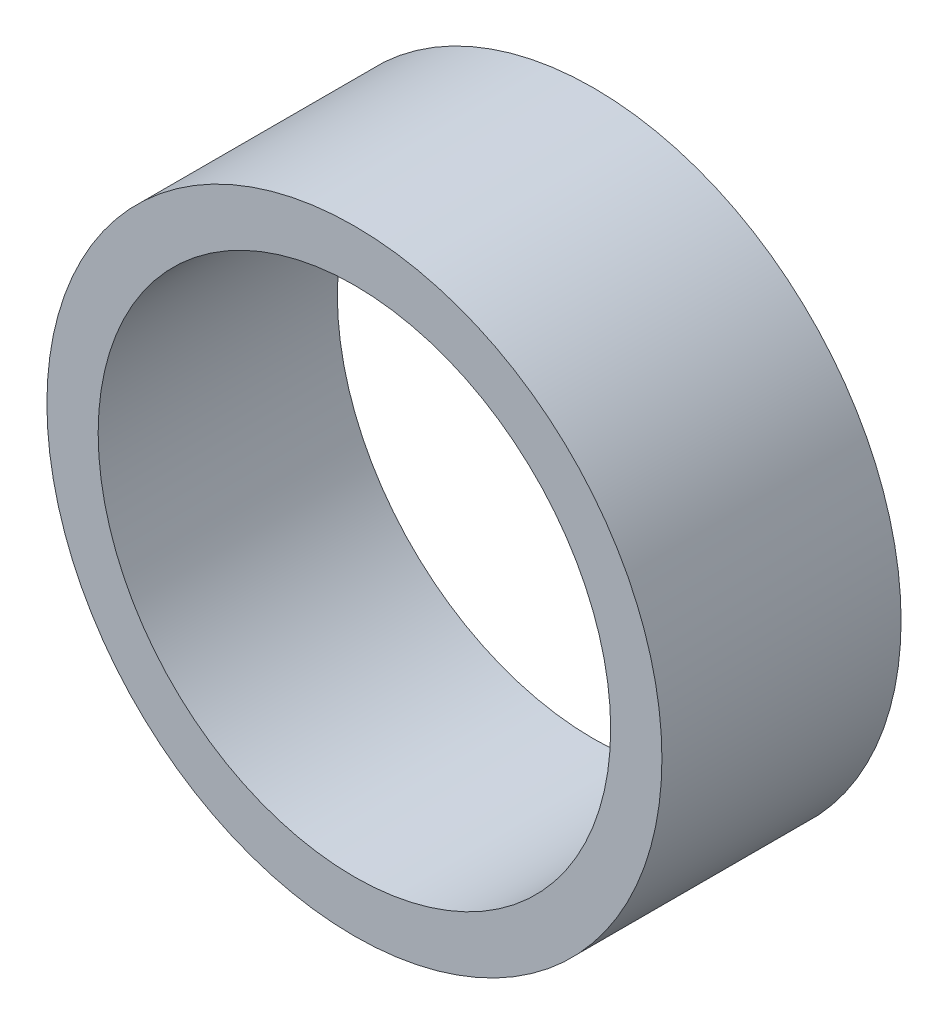
SolidWorks part; units mm, degrees
ref_plane "Plan de face" through (0, 0, 0) normal (0, 0, 1) x (1, 0, 0)
ref_plane "Plan de dessus" through (0, 0, 0) normal (0, 1, 0) x (1, 0, 0)
ref_plane "Plan de droite" through (0, 0, 0) normal (1, 0, 0) x (0, 0, -1)
sketch "Esquisse1" plane through (0, 0, 0) normal (0, 0, 1) x (1, 0, 0)
  circle A0 centre (0, 0) radius 9
  circle A1 centre (0, 0) radius 7.5
  dimension "D1" = 18
  dimension "D2" = 15
extrude "Boss.-Extru.1" add sketch "Esquisse1" along normal blind 7
